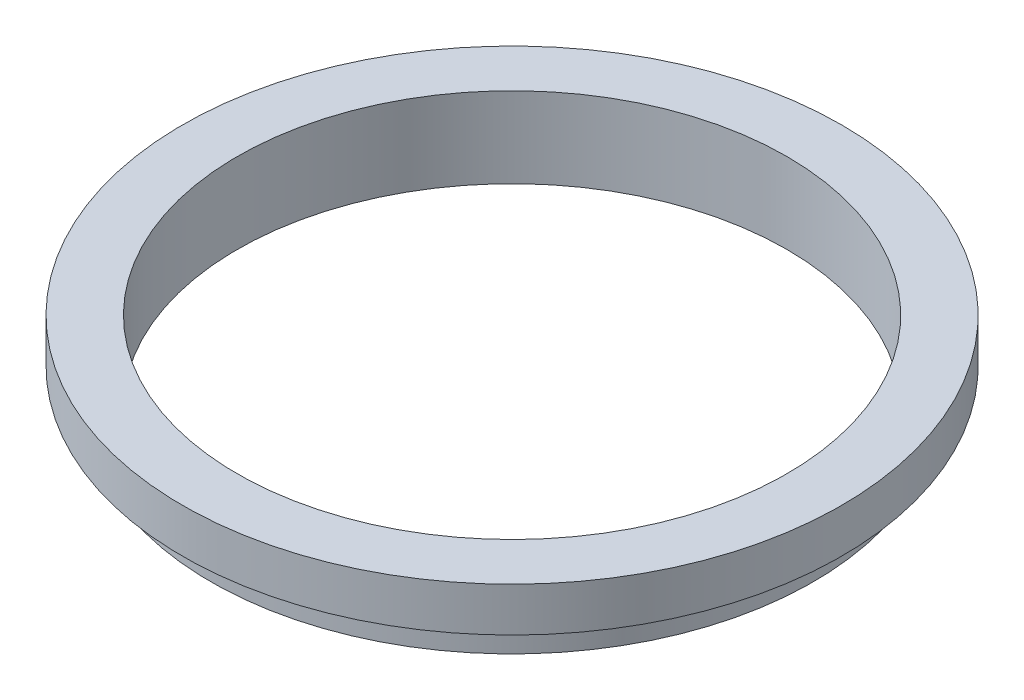
SolidWorks part; units mm, degrees
ref_plane "Plan de face" through (0, 0, 0) normal (0, 0, 1) x (1, 0, 0)
ref_plane "Plan de dessus" through (0, 0, 0) normal (0, 1, 0) x (1, 0, 0)
ref_plane "Plan de droite" through (0, 0, 0) normal (1, 0, 0) x (0, 0, -1)
sketch "Esquisse1" plane through (0, 0, 0) normal (0, 0, 1) x (1, 0, 0)
  line L0 (143.3965, 12.7) -> (142.494, 12.7)
  line L1 (142.494, 0) -> (130.048, 0)
  line L2 (130.048, 0) -> (130.048, 38.1)
  line L3 (130.048, 38.1) -> (155.956, 38.1)
  line L4 (155.956, 38.1) -> (155.956, 17.2602)
  line L5 (142.494, 12.7) -> (142.494, 0)
  line L6 (0, 0) -> (0, 38.1) construction
  line L7 (149.6762, 17.2602) -> (155.956, 17.2602)
  arc A0 (149.6762, 17.2602) -> (143.3965, 12.7) centre (149.6762, 10.6562) ccw
  dimension "D1" = 12.446
  dimension "D4" = 6.604
  dimension "D3" = 38.1
  dimension "D5" = 25.908
  dimension "D6" = 130.048
revolve "Révolution1" add sketch "Esquisse1" angle 360 about L6
